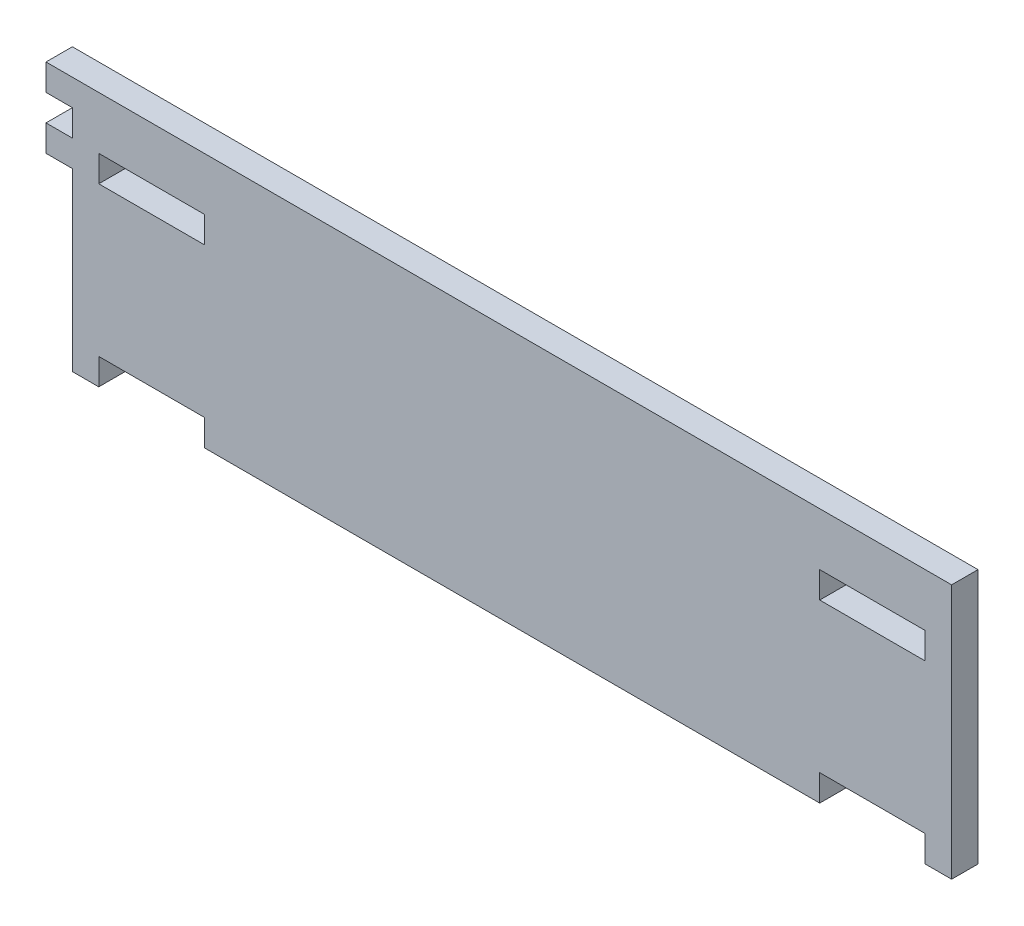
SolidWorks part; units mm, degrees
ref_plane "Alzado" through (0, 0, 0) normal (0, 0, 1) x (1, 0, 0)
ref_plane "Planta" through (0, 0, 0) normal (0, 1, 0) x (1, 0, 0)
ref_plane "Vista lateral" through (0, 0, 0) normal (1, 0, 0) x (0, 0, -1)
sketch "Croquis1" plane through (0, 0, 0) normal (0, 0, 1) x (1, 0, 0)
  line L0 (15, 20) -> (85, 20) construction
  line L1 (0, 0) -> (3, 0)
  line L2 (0, 0) -> (0, 29)
  line L3 (0, 29) -> (100, 29)
  line L4 (100, 0) -> (100, 29)
  line L6 (3, 0) -> (3, 3)
  line L7 (3, 3) -> (15, 3)
  line L8 (15, 0) -> (15, 3)
  line L10 (85, 0) -> (85, 3)
  line L11 (85, 3) -> (97, 3)
  line L12 (97, 0) -> (97, 3)
  line L13 (3, 23) -> (15, 23)
  line L14 (3, 23) -> (3, 20)
  line L15 (3, 20) -> (15, 20)
  line L16 (15, 23) -> (15, 20)
  line L17 (85, 23) -> (97, 23)
  line L18 (85, 23) -> (85, 20)
  line L19 (85, 20) -> (97, 20)
  line L20 (97, 23) -> (97, 20)
  line L34 (15, 0) -> (85, 0)
  line L35 (97, 0) -> (100, 0)
  dimension "D1" = 3
  dimension "D2" = 12
  dimension "D3" = 3
  dimension "D4" = 100
  dimension "D5" = 3
  dimension "D6" = 29
  dimension "D7" = 12
  dimension "D8" = 12
  dimension "D9" = 20
  dimension "D10" = 3
  dimension "D11" = 3
  dimension "D12" = 3
  dimension "D13" = 3
extrude "Saliente-Extruir1" add sketch "Croquis1" along normal blind 3
sketch "Croquis2" plane through (0, 0, 3) normal (0, 0, 1) x (1, 0, 0)
  line L0 (0, 29) -> (0, 0) construction
  line L1 (0, 23) -> (-3, 23)
  line L2 (0, 23) -> (0, 20)
  line L3 (0, 20) -> (-3, 20)
  line L4 (-3, 23) -> (-3, 20)
  line L5 (3, 20) -> (15, 20) construction
  line L7 (0, 29) -> (-3, 29)
  line L8 (0, 29) -> (0, 26)
  line L9 (0, 26) -> (-3, 26)
  line L10 (-3, 29) -> (-3, 26)
  dimension "D1" = 3
  dimension "D2" = 3
  dimension "D3" = 3
extrude "Saliente-Extruir2" add sketch "Croquis2" against normal blind 3
